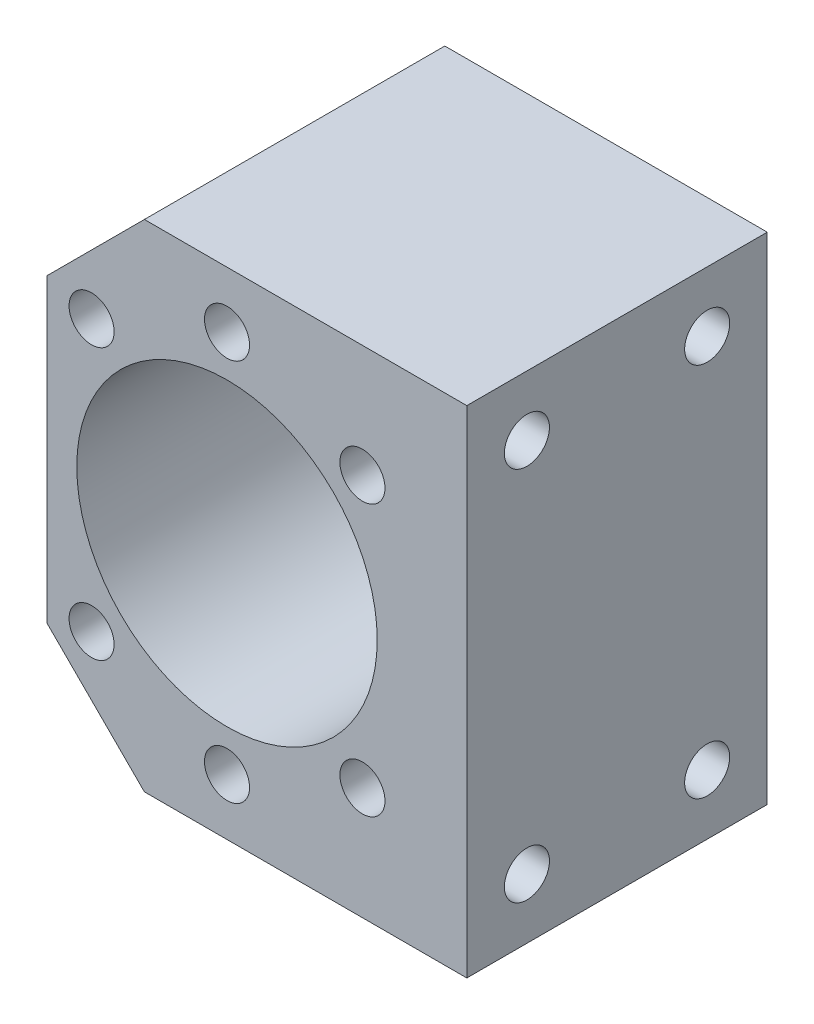
SolidWorks part; units mm, degrees
material "1060 Alloy"
ref_plane "Front Plane" through (0, 0, 0) normal (0, 0, 1) x (1, 0, 0)
ref_plane "Top Plane" through (0, 0, 0) normal (0, 1, 0) x (1, 0, 0)
ref_plane "Right Plane" through (0, 0, 0) normal (1, 0, 0) x (0, 0, -1)
sketch "Sketch1" plane through (0, 0, 0) normal (0, 0, 1) x (1, 0, 0)
  line L0 (-24, -20) -> (-11, -33)
  line L1 (-11, -33) -> (31.93, -33)
  line L2 (-24, -20) -> (-24, 20)
  line L3 (-11, 33) -> (31.93, 33)
  line L4 (31.93, -33) -> (31.93, 33)
  line L5 (-24, 20) -> (-24, 33) construction
  line L6 (-24, 33) -> (-11, 33) construction
  line L12 (-24, -20) -> (-11, -33) construction
  line L13 (-35.8332, 0) -> (27.1872, 0) construction
  line L14 (-24, 20) -> (-11, 33)
  circle A0 centre (0, 0) radius 20
  point P0 (0, 0)
  point P16 (-20.9054, -23.0946)
  point P28 (0, 0)
  dimension "D" = 40
  dimension "B" = 66
  dimension "H" = 55.93
  dimension "h1" = 24
  dimension "E" = 13
extrude "Boss-Extrude2" add sketch "Sketch1" along normal blind 40 contours L2 L14 L3 L4 L1 L0 | A0
sketch "Sketch8" plane through (0, 0, 40) normal (0, 0, 1) x (1, 0, 0)
  line L0 (-18.0312, -18.0312) -> (18.0312, 18.0312) construction
  line L1 (-18.0312, 18.0312) -> (18.0312, -18.0312) construction
  line L2 (0, 25.5) -> (0, -25.5) construction
  circle A1 centre (0, 25.5) radius 3
  circle A2 centre (18.0312, 18.0312) radius 3
  circle A4 centre (18.0312, -18.0312) radius 3
  circle A5 centre (0, -25.5) radius 3
  circle A6 centre (-18.0312, -18.0312) radius 3
  circle A8 centre (-18.0312, 18.0312) radius 3
  circle A9 centre (25.5, 0) radius 3 [skipped]
  circle A10 centre (-25.5, 0) radius 3 [skipped]
  point P22 (0, 0)
  dimension "D1" = 8
  dimension "Y" = 6
  dimension "W" = 51
extrude "Cut-Extrude1" cut sketch "Sketch8" against normal blind 16
sketch "Sketch9" plane through (31.93, 0, 0) normal (1, 0, 0) x (0, 0, -1)
  line L1 (0, 0) -> (-40, 0) construction
  line L2 (-40, -33) -> (-40, 33) construction
  line L10 (-32, 25) -> (-32, -25) construction
  line L11 (-8, 25) -> (-8, -25) construction
  line L12 (11.1909, 25) -> (-32, 25) construction
  line L13 (0, 0) -> (11.1909, 0) construction
  line L14 (11.1909, -25) -> (11.1909, 25) construction
  line L15 (11.1909, -25) -> (-32, -25) construction
  circle A1 centre (-32, 25) radius 3
  circle A2 centre (-8, 25) radius 3
  circle A3 centre (-8, -25) radius 3
  circle A4 centre (-32, -25) radius 3
  point P4 (-20, 0)
  point P8 (11.1909, 0)
  dimension "X" = 6
  dimension "C2" = 24
  dimension "C1" = 8
  dimension "P" = 50
extrude "Cut-Extrude2" cut sketch "Sketch9" against normal blind 16
chamfer "Chamfer1" [suppressed] distance 0.5 angle 45
